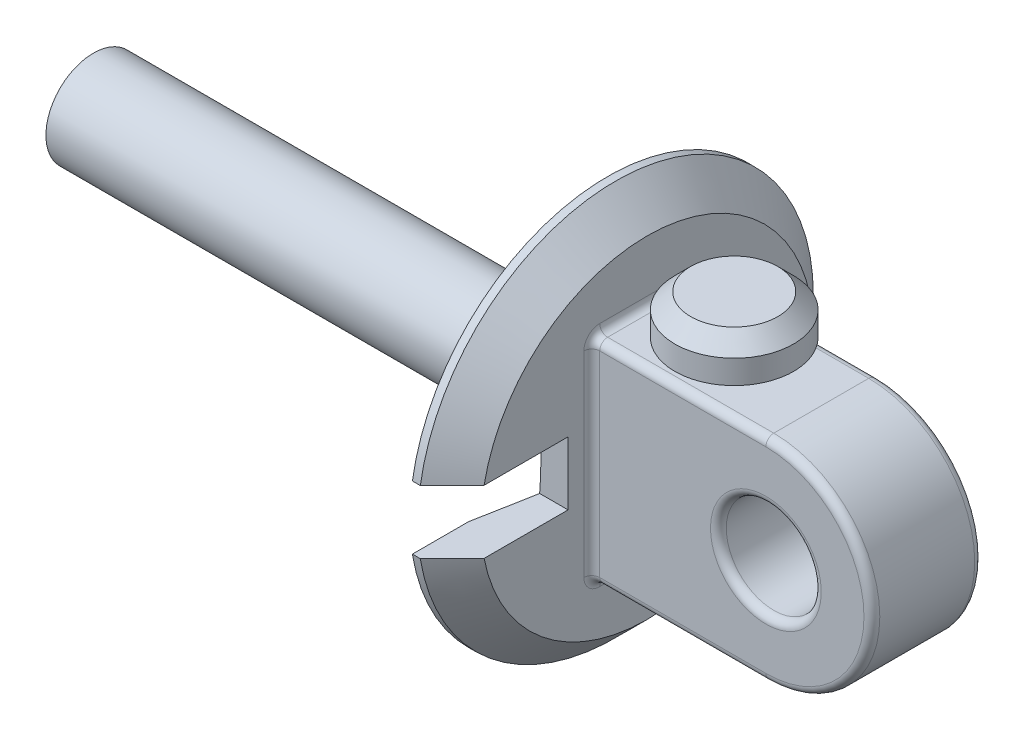
SolidWorks part; units mm, degrees
ref_plane "Front Plane" through (0, 0, 0) normal (0, 0, 1) x (1, 0, 0)
ref_plane "Top Plane" through (0, 0, 0) normal (0, 1, 0) x (1, 0, 0)
ref_plane "Right Plane" through (0, 0, 0) normal (1, 0, 0) x (0, 0, -1)
sketch "Sketch1" plane through (0, 0, 0) normal (0, 0, 1) x (1, 0, 0)
  line L0 (0, 13.4) -> (-22, 13.4)
  line L1 (0, -13.4) -> (-22, -13.4)
  line L2 (-22, 13.4) -> (-22, -13.4)
  circle A0 centre (0, 0) radius 6
  arc A1 (0, 13.4) -> (0, -13.4) centre (0, 0) cw
  dimension "D1" = 12
  dimension "D2" = 13.4
  dimension "D3" = 22
extrude "Boss-Extrude3" add sketch "Sketch1" along normal mid plane 14
sketch "Sketch6" plane through (-22, 0, 0) normal (-1, 0, 0) x (0, 0, 1)
  circle A0 centre (0, 0) radius 25
  dimension "D1" = 50
extrude "Boss-Extrude4" add sketch "Sketch6" along normal blind 5
sketch "Sketch7" plane through (0, 0, 0) normal (0, 0, 1) x (1, 0, 0)
  line L0 (-27, 0) -> (-23.5, 0)
  line L1 (-27, 25) -> (-27, -25) construction
  line L2 (-23.5, 0) -> (-27, -18)
  line L3 (-27, -18) -> (-27, 0)
  dimension "D1" = 18
  dimension "D2" = 3.5
revolve "Cut-Revolve2" cut sketch "Sketch7" angle 360 about L0
chamfer "Chamfer1" distance 4 angle 45 1 edges at (-22, 0, 25)
sketch "Sketch8" plane through (-22, 0, 0) normal (1, 0, 0) x (0, 0, -1)
  circle A0 centre (0, 0) radius 6
  dimension "D1" = 12
extrude "Boss-Extrude5" add sketch "Sketch8" against normal blind 70
sketch "Sketch9" plane through (0, 13.4, 0) normal (0, 1, 0) x (1, 0, 0)
  circle A0 centre (-11, 0) radius 3
  dimension "D1" = 6
extrude "Boss-Extrude6" add sketch "Sketch9" along normal blind 2
sketch "Sketch10" plane through (0, 15.4, 0) normal (0, 1, 0) x (1, 0, 0)
  circle A0 centre (-11, 0) radius 7.5
  dimension "D1" = 15
extrude "Boss-Extrude7" add sketch "Sketch10" along normal blind 5
chamfer "Chamfer2" distance 2 angle 45 1 edges at (-18.5, 20.4, 0)
sketch "Sketch13" plane through (-27, 0, 0) normal (-1, 0, 0) x (0, 0, 1)
  line L1 (10, -4) -> (40, -4)
  line L2 (10, -4) -> (10, 4)
  line L3 (10, 4) -> (40, 4)
  line L4 (40, -4) -> (40, 4)
  line L5 (10, -4) -> (40, 4) construction
  line L6 (10, 4) -> (40, -4) construction
  circle A0 centre (0, 0) radius 25 construction
  circle A1 centre (0, 0) radius 25 construction
  point P0 (25, 0)
  dimension "D1" = 30
  dimension "D2" = 8
extrude "Cut-Extrude1" cut sketch "Sketch13" against normal through all both and the other way through all
fillet "Fillet1" radius 1 12 edges at (-22, -13.4, 0) (-22, 13.4, 0) (6, 0, -7) (-11, 13.4, -7) (-22, 0, -7) (-11, -13.4, -7) (13.4, 0, -7) (6, 0, 7) (-11, -13.4, 7) (-22, 0, 7) (-11, 13.4, 7) (13.4, 0, 7)
